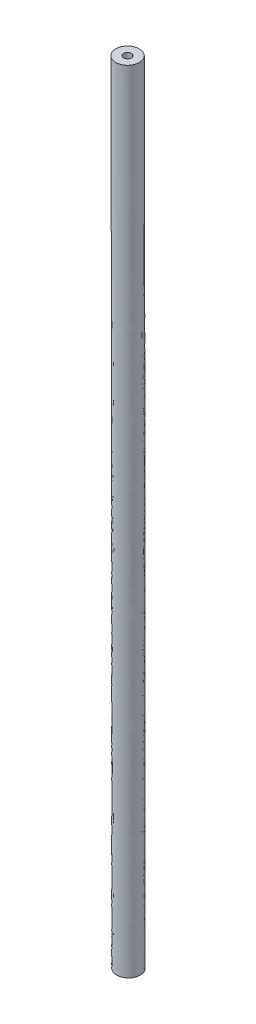
SolidWorks part; units mm, degrees
ref_plane "Front Plane" through (0, 0, 0) normal (0, 0, 1) x (1, 0, 0)
ref_plane "Top Plane" through (0, 0, 0) normal (0, 1, 0) x (1, 0, 0)
ref_plane "Right Plane" through (0, 0, 0) normal (1, 0, 0) x (0, 0, -1)
sketch "Sketch1" plane through (0, 0, 0) normal (0, 1, 0) x (1, 0, 0)
  circle A0 centre (0, 0) radius 1.5
  circle A1 centre (0, 0) radius 0.5
  dimension "D1" = 1
  dimension "D2" = 3
sketch "Sketch2" plane through (0, 0, 0) normal (0, 0, 1) x (1, 0, 0)
  line L0 (0, 25) -> (0, 0)
  line L3 (-0.0625, 75) -> (-0.125, 100)
  line L4 (0, 25) -> (0, 75) construction
  line L5 (0, 75) -> (0, 225) construction
  line L6 (0, 225) -> (0, 275) construction
  line L7 (-0.125, 100) -> (-0.4375, 225) construction
  arc A1 (0, 25) -> (-0.0625, 75) centre (-20000.0547, 25) ccw
  arc A2 (-0.4375, 225) -> (-0.5, 275) centre (19999.5547, 275) cw construction
  dimension "D1" = 50
  dimension "D2" = 150
  dimension "D3" = 25
  dimension "D4" = 25
  dimension "D5" = 0.5
sweep "Sweep1" add profiles "Sketch1" path "Sketch2"
sketch "Sketch4" plane through (0, 0, 0) normal (0, -1, 0) x (-1, 0, 0)
  point P0 (0, 0)
hole_wizard "Ø2.0mm Dowel Hole1" positions "Sketch4" profile "Sketch5" hole size "Ø2.0" standard "ANSI Metric"
sketch "Sketch5" plane through (0, 0, 0) normal (1, 0, 0) x (0, 0, -1)
  line L0 (0, 0) -> (0, 8.1009)
  line L1 (0, 8.1009) -> (1, 7.5)
  line L2 (1, 7.5) -> (1, 0)
  line L5 (1, 0) -> (0, 0)
  line L10 (0, 8.1009) -> (-1, 7.5) construction
  line L11 (0, -6.35) -> (0, 107.95) construction
  dimension "Hole Dia." = 2
  dimension "Hole Depth" = 7.5
  dimension "Drill Angle" = 118
